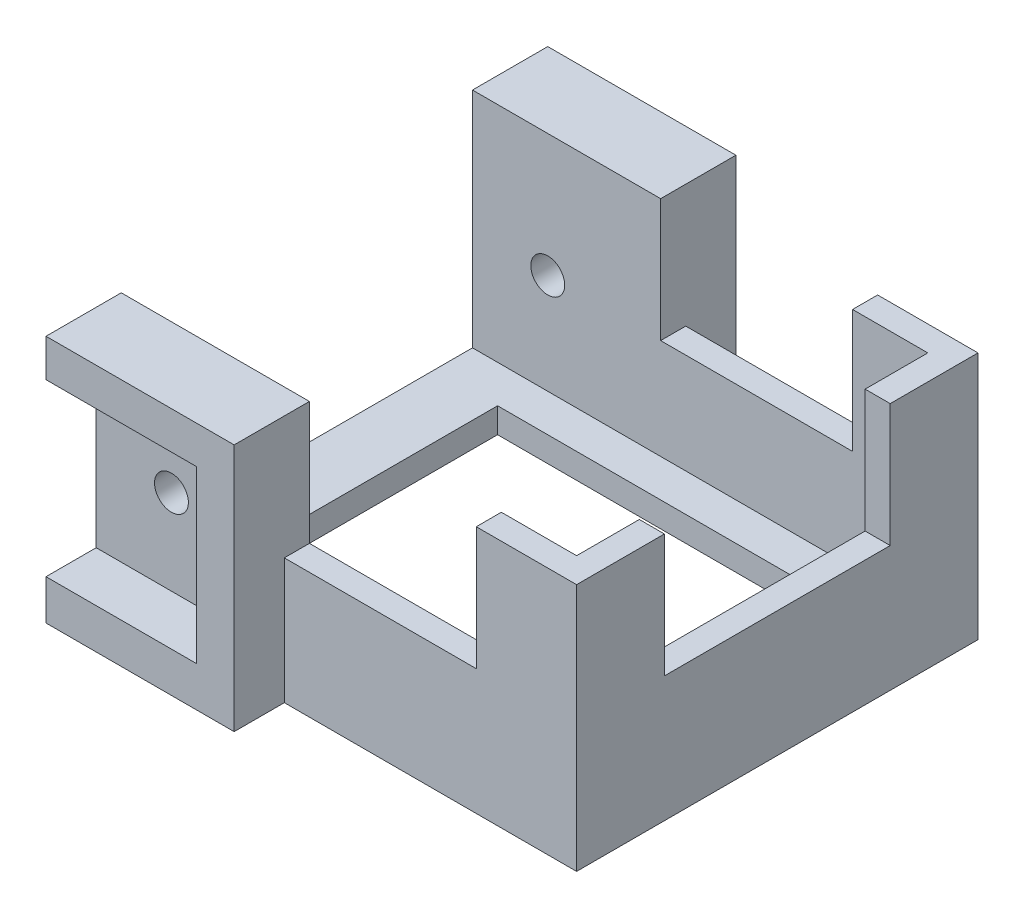
SolidWorks part; units mm, degrees
material "ABS"
ref_plane "Спереди" through (0, 0, 0) normal (0, 0, 1) x (1, 0, 0)
ref_plane "Сверху" through (0, 0, 0) normal (0, 1, 0) x (1, 0, 0)
ref_plane "Справа" through (0, 0, 0) normal (1, 0, 0) x (0, 0, -1)
sketch "Эскиз1" plane through (0, 0, 0) normal (0, 1, 0) x (1, 0, 0)
  line L1 (-19.15, 16) -> (19.15, 16)
  line L2 (-19.15, 16) -> (-19.15, -16)
  line L3 (-19.15, -16) -> (19.15, -16)
  line L4 (19.15, 16) -> (19.15, -16)
  line L5 (-19.15, 16) -> (19.15, -16) construction
  line L6 (-19.15, -16) -> (19.15, 16) construction
  point P0 (0, 0)
  dimension "D1" = 32
  dimension "D2" = 38.3
extrude "Бобышка-Вытянуть1" add sketch "Эскиз1" along normal blind 2
sketch "Эскиз2" plane through (0, 2, 0) normal (0, 1, 0) x (1, 0, 0)
  line L0 (-19.15, 16) -> (19.15, 16)
  line L1 (19.15, 16) -> (19.15, -16)
  line L3 (19.15, -16) -> (-19.15, -16)
  line L4 (-19.15, -16) -> (-19.15, -14)
  line L5 (-19.15, 16) -> (-19.15, -16) construction
  line L6 (-19.15, -14) -> (17.15, -14)
  line L7 (17.15, -14) -> (17.15, 14)
  line L8 (17.15, 14) -> (-19.15, 14)
  line L9 (-19.15, 14) -> (-19.15, 16)
  line L10 (17.15, 14) -> (19.15, 14) construction
  dimension "D1" = 2
extrude "Бобышка-Вытянуть2" add sketch "Эскиз2" along normal blind 75
sketch "Эскиз9" plane through (0, 0, 16) normal (0, 0, 1) x (1, 0, 0)
  line L0 (-19.15, 77) -> (-19.15, 0) construction
  line L1 (-19.15, 0) -> (19.15, 0) construction
  circle A0 centre (-13.15, 69) radius 1.35
  circle A1 centre (-13.15, 10) radius 1.35
  dimension "D1" = 2.7
  dimension "D2" = 59
  dimension "D3" = 6
  dimension "D4" = 10
extrude "Вырез-Вытянуть5" cut sketch "Эскиз9" against normal through all
sketch "Эскиз10" plane through (0, 0, 16) normal (0, 0, 1) x (1, 0, 0)
  line L0 (19.15, 77) -> (19.15, 0) construction
  line L1 (-4.15, 62) -> (11.15, 62)
  line L2 (-4.15, 62) -> (-4.15, 10)
  line L3 (-4.15, 10) -> (11.15, 10)
  line L4 (11.15, 62) -> (11.15, 10)
  line L5 (-19.15, 0) -> (19.15, 0) construction
  line L6 (-19.15, 77) -> (19.15, 77) construction
  line L7 (-19.15, 77) -> (-19.15, 0) construction
  dimension "D1" = 8
  dimension "D2" = 10
  dimension "D3" = 15
  dimension "D4" = 15
extrude "Вырез-Вытянуть6" cut sketch "Эскиз10" against normal through all
sketch "Эскиз11" plane through (0, 0, 0) normal (0, -1, 0) x (1, 0, 0)
  line L0 (-14.15, 11) -> (14.15, 11)
  line L1 (-19.15, 16) -> (19.15, 16) construction
  line L2 (-19.15, 16) -> (-19.15, -16) construction
  line L3 (-19.15, -16) -> (19.15, -16) construction
  line L4 (19.15, 16) -> (19.15, -16) construction
  line L5 (14.15, 11) -> (14.15, -11)
  line L6 (-14.15, -11) -> (14.15, -11)
  line L7 (-14.15, 11) -> (-14.15, -11)
  dimension "D1" = 5
extrude "Вырез-Вытянуть7" cut sketch "Эскиз11" against normal through all
sketch "Эскиз13" plane through (19.15, 0, 0) normal (1, 0, 0) x (0, 0, -1)
  line L1 (-9, 67) -> (9, 67)
  line L2 (-9, 67) -> (-9, 10)
  line L3 (-9, 10) -> (9, 10)
  line L4 (9, 67) -> (9, 10)
  line L5 (-16, 77) -> (16, 77) construction
  line L6 (-9, 67) -> (-16, 67) construction
  line L7 (-16, 77) -> (-16, 0) construction
  line L8 (-16, 0) -> (16, 0) construction
  line L9 (-16, 77) -> (-16, 0) construction
  line L10 (9, 67) -> (16, 67) construction
  line L11 (16, 77) -> (16, 0) construction
  dimension "D1" = 7
  dimension "D2" = 10
  dimension "D3" = 10
extrude "Вырез-Вытянуть8" cut sketch "Эскиз13" against normal through all
sketch "Эскиз14" plane through (0, 0, -16) normal (0, 0, -1) x (-1, 0, 0)
  line L0 (-19.15, 77) -> (19.15, 77) construction
  line L1 (-14.15, 72) -> (-9.15, 72)
  line L2 (-14.15, 72) -> (-14.15, 70)
  line L3 (-14.15, 70) -> (-9.15, 70)
  line L4 (-9.15, 72) -> (-9.15, 70)
  line L5 (-0.85, 72) -> (4.15, 72)
  line L6 (-0.85, 72) -> (-0.85, 70)
  line L7 (-0.85, 70) -> (4.15, 70)
  line L8 (4.15, 72) -> (4.15, 70)
  line L9 (-19.15, 77) -> (-19.15, 0) construction
  line L10 (19.15, 77) -> (19.15, 0) construction
  dimension "D1" = 5
  dimension "D2" = 2
  dimension "D3" = 5
  dimension "D4" = 5
  dimension "D5" = 15
extrude "Вырез-Вытянуть9" cut sketch "Эскиз14" against normal through all
sketch "Эскиз16" plane through (0, 0, 16) normal (0, 0, 1) x (1, 0, 0)
  line L0 (-19.15, 77) -> (-19.15, 0) construction
  line L1 (-19.15, 0) -> (-4.15, 0)
  line L2 (-19.15, 0) -> (-19.15, 3.2)
  line L3 (-19.15, 3.2) -> (-7.15, 3.2)
  line L4 (-7.15, 16.8) -> (-7.15, 3.2)
  line L5 (-19.15, 16.8) -> (-7.15, 16.8)
  line L6 (-19.15, 16.8) -> (-19.15, 19.8)
  line L7 (-19.15, 19.8) -> (-4.15, 19.8)
  line L8 (-4.15, 19.8) -> (-4.15, 0)
  line L9 (-4.15, 62) -> (-4.15, 10) construction
  dimension "D1" = 3.2
  dimension "D2" = 3
  dimension "D3" = 13.6
  dimension "D4" = 3
extrude "Бобышка-Вытянуть3" add sketch "Эскиз16" along normal blind 4
mirror "Зеркальное отражение1" about plane through (0, 0, 0) normal (0, 0, 1) of "Бобышка-Вытянуть3"
sketch "Эскиз17" plane through (0, 77, 0) normal (0, 1, 0) x (1, 0, 0)
  line L1 (-19.15, 16) -> (19.15, 16)
  line L2 (-19.15, 16) -> (-19.15, -16)
  line L3 (-19.15, -16) -> (19.15, -16)
  line L4 (19.15, 16) -> (19.15, -16)
extrude "Вырез-Вытянуть10" cut sketch "Эскиз17" against normal up to surface (57.2 mm away) up to face at (-11.65, 19.8, 18)
